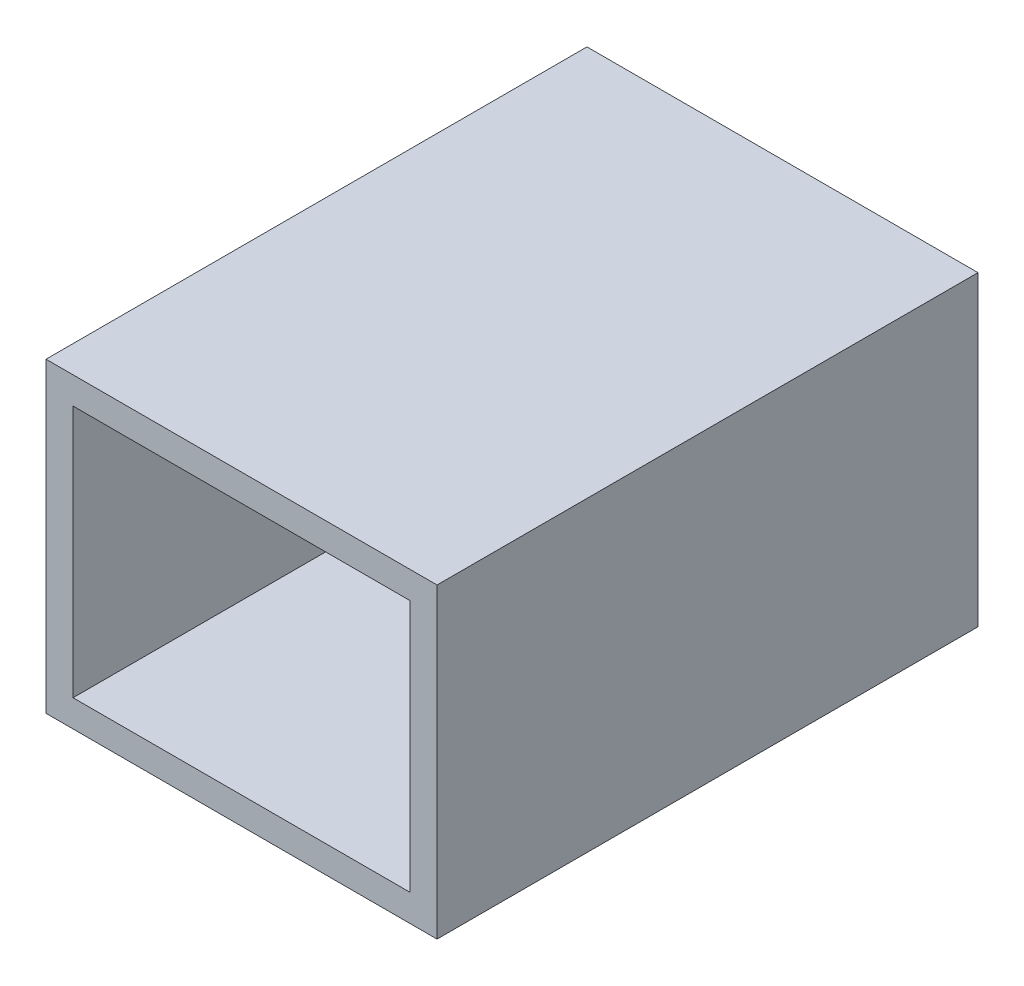
SolidWorks part; units mm, degrees
ref_plane "Alzado" through (0, 0, 0) normal (0, 0, 1) x (1, 0, 0)
ref_plane "Planta" through (0, 0, 0) normal (0, 1, 0) x (1, 0, 0)
ref_plane "Vista lateral" through (0, 0, 0) normal (1, 0, 0) x (0, 0, -1)
sketch "Croquis1" plane through (0, 0, 0) normal (0, 0, 1) x (1, 0, 0)
  line L1 (-72.2836, -56.6957) -> (72.2836, -56.6957)
  line L2 (-72.2836, -56.6957) -> (-72.2836, 56.6957)
  line L3 (-72.2836, 56.6957) -> (72.2836, 56.6957)
  line L4 (72.2836, -56.6957) -> (72.2836, 56.6957)
  line L5 (-72.2836, -56.6957) -> (72.2836, 56.6957) construction
  line L6 (-72.2836, 56.6957) -> (72.2836, -56.6957) construction
  point P0 (0, 0)
extrude "Saliente-Extruir1" add sketch "Croquis1" along normal blind 200
shell "Vaciado2" thickness 10
